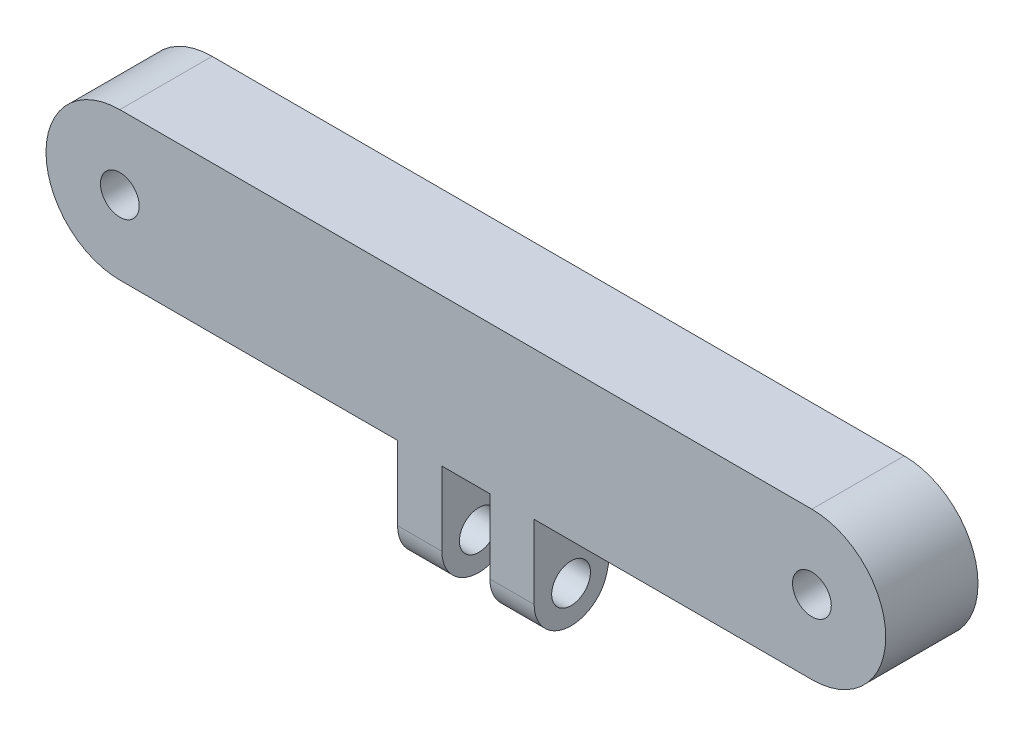
SolidWorks part; units mm, degrees
ref_plane "Front Plane" through (0, 0, 0) normal (0, 0, 1) x (1, 0, 0)
ref_plane "Top Plane" through (0, 0, 0) normal (0, 1, 0) x (1, 0, 0)
ref_plane "Right Plane" through (0, 0, 0) normal (1, 0, 0) x (0, 0, -1)
sketch "Sketch1" plane through (0, 0, 0) normal (0, 0, 1) x (1, 0, 0)
  line L0 (-37.5, 0) -> (37.5, 0) construction
  line L5 (-37.5, 8) -> (37.5, 8)
  line L6 (-37.5, -8) -> (37.5, -8)
  arc A0 (-37.5, 8) -> (-37.5, -8) centre (-37.5, 0) ccw
  arc A1 (37.5, -8) -> (37.5, 8) centre (37.5, 0) ccw
  circle A2 centre (-37.5, 0) radius 2.1
  circle A3 centre (37.5, 0) radius 2.1
  point P2 (0, 0)
  dimension "D2" = 8
  dimension "D3" = 4.2
  dimension "D1" = 75
extrude "Boss-Extrude1" add sketch "Sketch1" along normal blind 10
shell "Shell2" thickness 3
sketch "Sketch2" plane through (0, 0, 0) normal (1, 0, 0) x (0, 0, -1)
  line L0 (-10, -8) -> (-10, -16)
  line L1 (-2.1072, -16.9196) -> (0, -8)
  line L2 (0, -8) -> (-10, -8)
  arc A0 (-10, -16) -> (-2.1072, -16.9196) centre (-6, -16) ccw
  circle A1 centre (-6, -16) radius 2.1
  point P6 (0, 0)
  point P10 (0, 0)
  dimension "D1" = 4
  dimension "D2" = 4.2
  dimension "D3" = 8
extrude "Boss-Extrude2" add sketch "Sketch2" along normal mid plane 14.8
sketch "Sketch3" plane through (0, 0, 10) normal (0, 0, 1) x (1, 0, 0)
  line L0 (-7.4, -20) -> (7.4, -20) construction
  line L1 (-2.6, -8) -> (2.6, -8)
  line L2 (-2.6, -8) -> (-2.6, -22)
  line L3 (-2.6, -22) -> (2.6, -22)
  line L4 (2.6, -8) -> (2.6, -22)
  line L5 (-37.5, -8) -> (-7.4, -8) construction
  point P8 (0, -8)
  dimension "D1" = 5.2
  dimension "D2" = 2
extrude "Cut-Extrude1" cut sketch "Sketch3" against normal through all both
